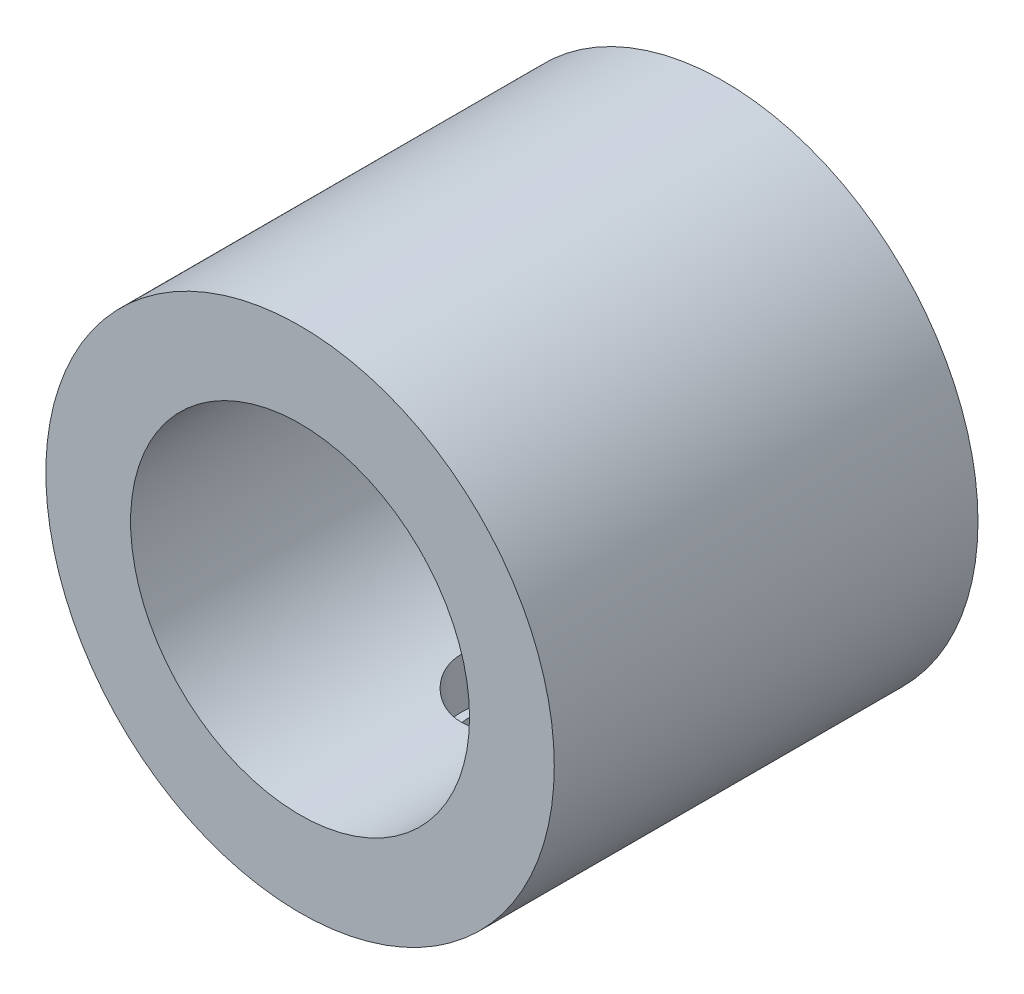
SolidWorks part; units mm, degrees
ref_plane "前视基准面" through (0, 0, 0) normal (0, 0, 1) x (1, 0, 0)
ref_plane "上视基准面" through (0, 0, 0) normal (0, 1, 0) x (1, 0, 0)
ref_plane "右视基准面" through (0, 0, 0) normal (1, 0, 0) x (0, 0, -1)
sketch "草图1" plane through (0, 0, 0) normal (0, 0, 1) x (1, 0, 0)
  circle A0 centre (0, 0) radius 2
  circle A1 centre (0, 0) radius 3
extrude "凸台-拉伸1" add sketch "草图1" along normal blind 5
sketch "草图2" plane through (0, 0, 0) normal (0, 1, 0) x (1, 0, 0)
  line L0 (-3, 0) -> (3, -5) construction
  line L1 (-3, -5) -> (3, 0) construction
  circle A0 centre (0, -2.5) radius 0.5
extrude "切除-拉伸1" cut sketch "草图2" against normal blind 5
sketch "草图3" plane through (0, 0, 0) normal (0, 1, 0) x (1, 0, 0)
  line L0 (-3, 0) -> (3, -5) construction
  circle A0 centre (0, -2.5) radius 0.6
extrude "切除-拉伸2" cut sketch "草图3" against normal blind 2.5
